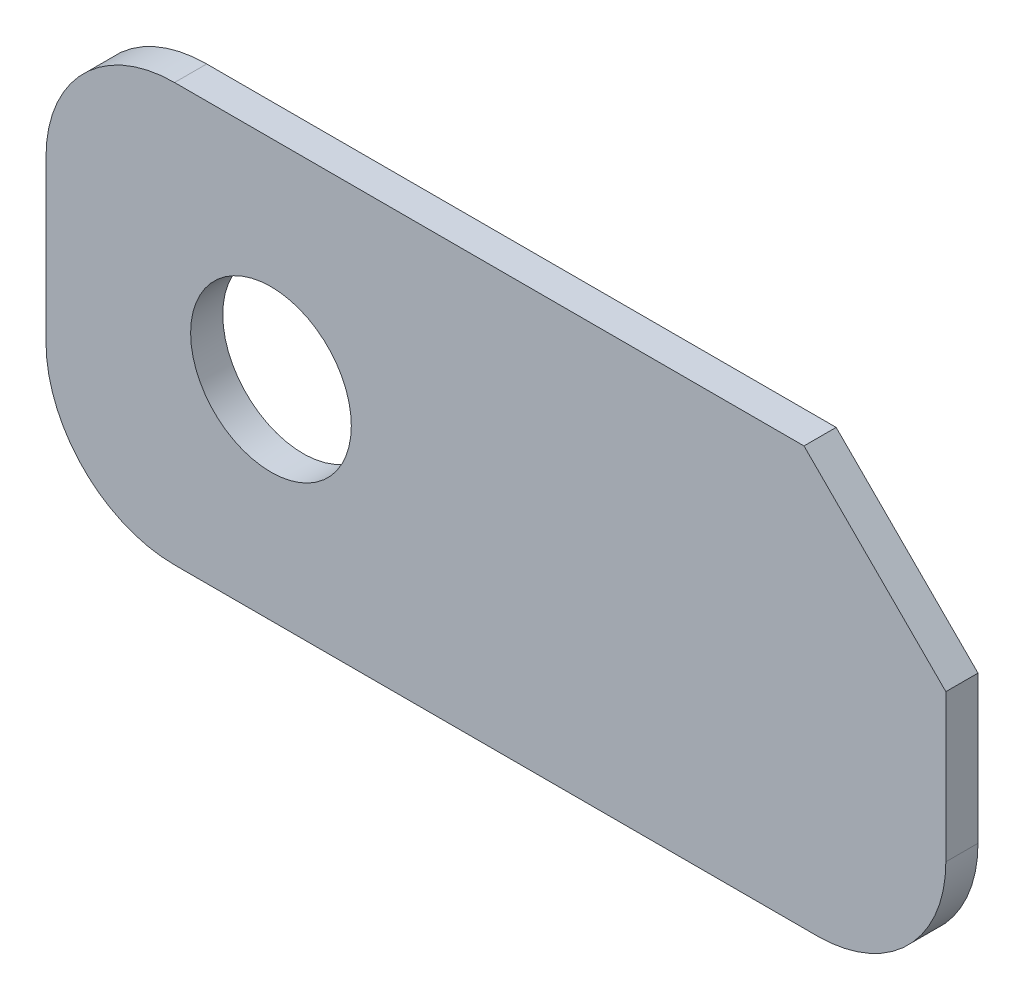
SolidWorks part; units mm, degrees
ref_plane "Front Plane" through (0, 0, 0) normal (0, 0, 1) x (1, 0, 0)
ref_plane "Top Plane" through (0, 0, 0) normal (0, 1, 0) x (1, 0, 0)
ref_plane "Right Plane" through (0, 0, 0) normal (1, 0, 0) x (0, 0, -1)
sketch "Sketch1" plane through (0, 0, 0) normal (0, 0, 1) x (1, 0, 0)
  line L0 (-50.7689, -2.9037) -> (-11.5974, -2.9037)
  line L1 (-11.5974, -2.9037) -> (-2.7689, -11.7322)
  line L2 (-2.7689, -11.7322) -> (-2.7689, -20.9037)
  line L3 (-10.7689, -28.9037) -> (-50.7689, -28.9037)
  line L4 (-58.7689, -20.9037) -> (-58.7689, -10.9037)
  arc A0 (-10.7689, -28.9037) -> (-2.7689, -20.9037) centre (-10.7689, -20.9037) ccw
  arc A1 (-50.7689, -2.9037) -> (-58.7689, -10.9037) centre (-50.7689, -10.9037) ccw
  arc A2 (-58.7689, -20.9037) -> (-50.7689, -28.9037) centre (-50.7689, -20.9037) ccw
extrude "Boss-Extrude1" add sketch "Sketch1" along normal blind 2 contours L0 L1 L2 A0 L3 A2 L4 A1
sketch "Sketch2" plane through (0, 0, 0) normal (0, 0, -1) x (-1, 0, 0)
  line L0 (58.7689, -15.9037) -> (2.7689, -15.9037) construction
  line L1 (58.7689, -20.9037) -> (58.7689, -10.9037) construction
  line L2 (2.7689, -11.7322) -> (2.7689, -20.9037) construction
  line L3 (30.7689, -28.9037) -> (30.7689, -2.9037) construction
  line L4 (10.7689, -28.9037) -> (50.7689, -28.9037) construction
  line L5 (50.7689, -2.9037) -> (11.5974, -2.9037) construction
  line L6 (30.7689, -15.9037) -> (58.7689, -15.9037) construction
  line L7 (44.7689, -2.9037) -> (44.7689, -28.9037) construction
  circle A0 centre (44.7689, -15.9037) radius 5
extrude "Cut-Extrude1" cut sketch "Sketch2" against normal blind 4.1
